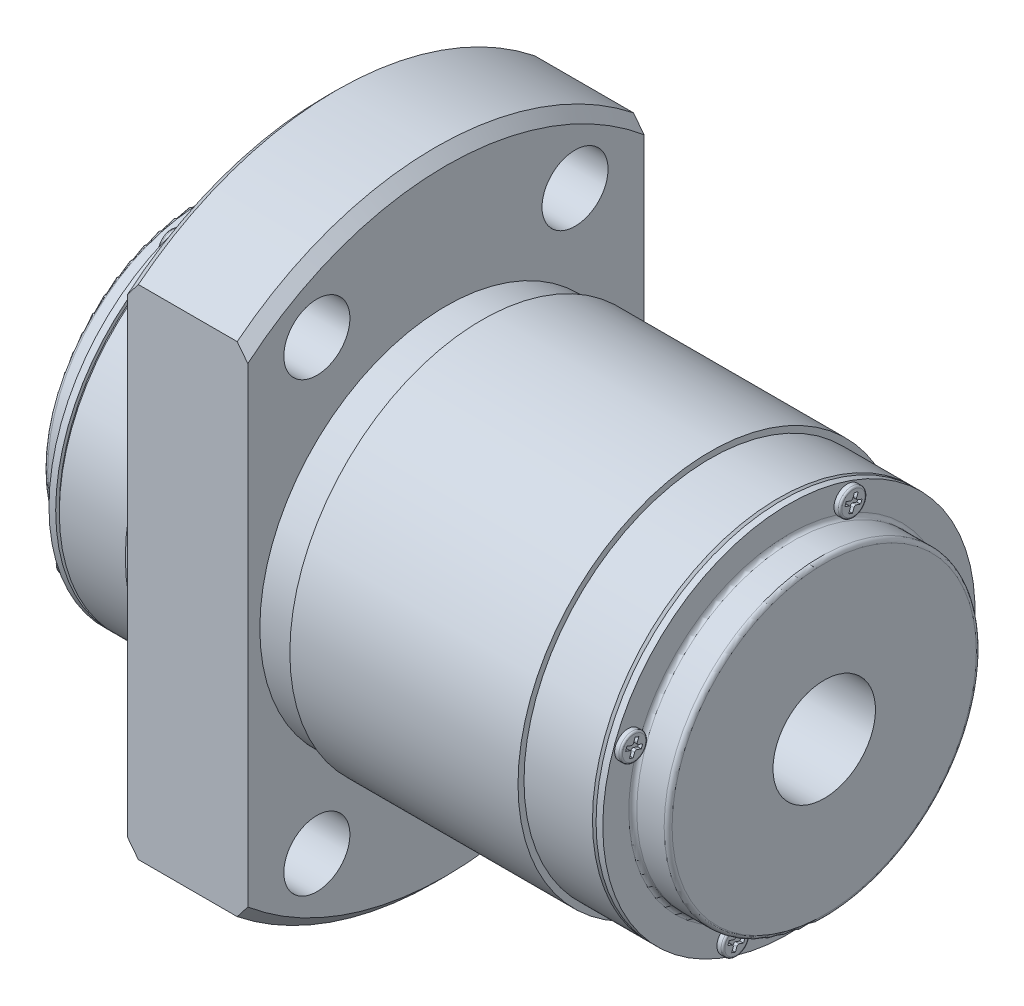
SolidWorks part; units mm, degrees
ref_plane "Front Plane" through (0, 0, 0) normal (0, 0, 1) x (1, 0, 0)
ref_plane "Top Plane" through (0, 0, 0) normal (0, 1, 0) x (1, 0, 0)
ref_plane "Right Plane" through (0, 0, 0) normal (1, 0, 0) x (0, 0, -1)
ref_plane "Plane1" through (0, 0, 0) normal (0, 0, 1) x (1, 0, 0)
sketch "Sketch1" plane through (0, 0, 0) normal (0, 0, 1) x (1, 0, 0)
  line L0 (-3.5, 7.5) -> (48.5, 7.5)
  line L1 (48.5, 7.5) -> (48.5, 12.67)
  line L2 (48.17, 13) -> (45.89, 13)
  line L3 (45.56, 13.33) -> (45.56, 15.5)
  line L4 (45.56, 15.5) -> (45, 15.5)
  line L5 (45, 15.5) -> (45, 15.2)
  line L6 (45, 15.2) -> (44.7, 15.5)
  line L7 (44.7, 15.5) -> (39, 15.5)
  line L8 (39, 15.5) -> (39, 16)
  line L9 (39, 16) -> (20, 16)
  line L10 (20, 16) -> (20, 15.5)
  line L11 (20, 15.5) -> (17, 15.5)
  line L12 (17, 15.5) -> (17, 25.6167)
  line L13 (17, 25.6167) -> (16.1167, 26.5)
  line L14 (16.1167, 26.5) -> (7.8833, 26.5)
  line L15 (7.8833, 26.5) -> (7, 25.6167)
  line L16 (7, 25.6167) -> (7, 16)
  line L17 (7, 16) -> (6.3, 16)
  line L18 (6.3, 16) -> (6.3, 15.5)
  line L19 (6.3, 15.5) -> (0.3, 15.5)
  line L20 (0.3, 15.5) -> (0, 15.2)
  line L21 (0, 15.2) -> (0, 15.5)
  line L22 (0, 15.5) -> (-0.56, 15.5)
  line L23 (-0.56, 15.5) -> (-0.56, 13.33)
  line L24 (-0.89, 13) -> (-3.17, 13)
  line L25 (-3.5, 12.67) -> (-3.5, 7.5)
  line L26 (45, 0) -> (0, 0) construction
  arc A0 (48.5, 12.67) -> (48.17, 13) centre (48.17, 12.67) ccw
  arc A1 (45.89, 13) -> (45.56, 13.33) centre (45.89, 13.33) cw
  arc A2 (-0.56, 13.33) -> (-0.89, 13) centre (-0.89, 13.33) cw
  arc A3 (-3.17, 13) -> (-3.5, 12.67) centre (-3.17, 12.67) ccw
revolve "Revolve1" add sketch "Sketch1" angle 360 about L26
ref_plane "Plane2" through (0, 0, 0) normal (0, -0.5, 0.866) x (1, 0, 0)
sketch "Sketch2" plane through (0, 0, 0) normal (0, -0.5, 0.866) x (1, 0, 0)
  line L0 (7, 21.5) -> (7, 24.25)
  line L1 (7, 24.25) -> (17, 24.25)
  line L2 (17, 24.25) -> (17, 21.5)
  line L3 (17, 21.5) -> (7, 21.5)
  line L4 (17, 21.5) -> (7, 21.5) construction
revolve "Cut-Revolve1" cut sketch "Sketch2" angle 360 about L4
ref_plane "Plane3" through (0, 0, 0) normal (0, -0.5, 0.866) x (1, 0, 0)
sketch "Sketch3" plane through (0, 0, 0) normal (0, -0.5, 0.866) x (1, 0, 0)
  line L0 (7, -21.5) -> (7, -18.75)
  line L1 (7, -18.75) -> (17, -18.75)
  line L2 (17, -18.75) -> (17, -21.5)
  line L3 (17, -21.5) -> (7, -21.5)
  line L4 (17, -21.5) -> (7, -21.5) construction
revolve "Cut-Revolve2" cut sketch "Sketch3" angle 360 about L4
ref_plane "Plane4" through (0, 0, 0) normal (0, 0.5, 0.866) x (1, 0, 0)
sketch "Sketch4" plane through (0, 0, 0) normal (0, 0.5, 0.866) x (1, 0, 0)
  line L0 (7, 21.5) -> (7, 24.25)
  line L1 (7, 24.25) -> (17, 24.25)
  line L2 (17, 24.25) -> (17, 21.5)
  line L3 (17, 21.5) -> (7, 21.5)
  line L4 (17, 21.5) -> (7, 21.5) construction
revolve "Cut-Revolve3" cut sketch "Sketch4" angle 360 about L4
ref_plane "Plane5" through (0, 0, 0) normal (0, 0.5, 0.866) x (1, 0, 0)
sketch "Sketch5" plane through (0, 0, 0) normal (0, 0.5, 0.866) x (1, 0, 0)
  line L0 (7, -21.5) -> (7, -18.75)
  line L1 (7, -18.75) -> (17, -18.75)
  line L2 (17, -18.75) -> (17, -21.5)
  line L3 (17, -21.5) -> (7, -21.5)
  line L4 (17, -21.5) -> (7, -21.5) construction
revolve "Cut-Revolve4" cut sketch "Sketch5" angle 360 about L4
ref_plane "Plane6" through (0, 0, 0) normal (0, 0, 1) x (1, 0, 0)
sketch "Sketch6" plane through (0, 0, 0) normal (0, 0, 1) x (1, 0, 0)
  line L0 (12, -5.5) -> (14.4585, -6.9194)
  line L1 (14.4585, -6.9194) -> (14.4585, -25.9585)
  line L2 (14.4585, -25.9585) -> (15, -26.5)
  line L3 (15, -26.5) -> (12, -26.5)
  line L4 (12, -26.5) -> (12, -5.5)
  line L5 (12, -26.5) -> (12, -5.5) construction
revolve "Cut-Revolve5" cut sketch "Sketch6" angle 360 about L5
ref_plane "Plane7" through (17, 0, 0) normal (1, 0, 0) x (0, 0, -1)
sketch "Sketch7" plane through (17, 0, 0) normal (1, 0, 0) x (0, 0, -1)
  line L0 (-33, 53) -> (-33, -53)
  line L1 (-33, -53) -> (33, -53)
  line L2 (33, -53) -> (33, 53)
  line L3 (33, 53) -> (-33, 53)
  line L4 (-16.5, 27.5) -> (-16.5, -27.5)
  line L5 (-16.5, -27.5) -> (16.5, -27.5)
  line L6 (16.5, -27.5) -> (16.5, 27.5)
  line L7 (16.5, 27.5) -> (-16.5, 27.5)
extrude "Cut-Extrude1" cut sketch "Sketch7" against normal blind 10
ref_plane "Plane8" through (0, 0, 0) normal (0, -0.342, 0.9397) x (1, 0, 0)
sketch "Sketch8" plane through (0, 0, 0) normal (0, -0.342, 0.9397) x (1, 0, 0)
  line L0 (-1.06, 14.25) -> (-1.06, 15.17)
  line L1 (-0.86, 15.37) -> (-0.56, 15.37)
  line L2 (-0.56, 15.37) -> (-0.56, 14.25)
  line L3 (-0.56, 14.25) -> (-1.06, 14.25)
  line L4 (-0.56, 14.25) -> (-1.06, 14.25) construction
  arc A0 (-1.06, 15.17) -> (-0.86, 15.37) centre (-0.86, 15.17) cw
revolve "Revolve2" add sketch "Sketch8" angle 360 about L4
ref_plane "Plane9" through (0, -4.8738, 13.3906) normal (0, -0.342, 0.9397) x (1, 0, 0)
sketch "Sketch9" plane through (0, -4.8738, 13.3906) normal (0, -0.342, 0.9397) x (1, 0, 0)
  line L0 (-1.06, 0) -> (-1.06, 0.92)
  line L1 (-0.86, 1.12) -> (-0.56, 1.12)
  line L2 (-0.56, 1.12) -> (-0.56, 0)
  line L3 (-0.56, 0) -> (-1.06, 0)
  line L4 (-0.56, 0) -> (-1.06, 0) construction
  arc A0 (-1.06, 0.92) -> (-0.86, 1.12) centre (-0.86, 0.92) cw
revolve "Revolve3" add sketch "Sketch9" angle 360 about L4
ref_plane "Plane10" through (0, 0, 0) normal (0, -0.342, 0.9397) x (1, 0, 0)
sketch "Sketch10" plane through (0, 0, 0) normal (0, -0.342, 0.9397) x (1, 0, 0)
  line L0 (-1.06, -14.25) -> (-1.06, -13.33)
  line L1 (-0.86, -13.13) -> (-0.56, -13.13)
  line L2 (-0.56, -13.13) -> (-0.56, -14.25)
  line L3 (-0.56, -14.25) -> (-1.06, -14.25)
  line L4 (-0.56, -14.25) -> (-1.06, -14.25) construction
  arc A0 (-1.06, -13.33) -> (-0.86, -13.13) centre (-0.86, -13.33) cw
revolve "Revolve4" add sketch "Sketch10" angle 360 about L4
ref_plane "Plane11" through (0, 4.8738, -13.3906) normal (0, -0.342, 0.9397) x (1, 0, 0)
sketch "Sketch11" plane through (0, 4.8738, -13.3906) normal (0, -0.342, 0.9397) x (1, 0, 0)
  line L0 (-1.06, 0) -> (-1.06, 0.92)
  line L1 (-0.86, 1.12) -> (-0.56, 1.12)
  line L2 (-0.56, 1.12) -> (-0.56, 0)
  line L3 (-0.56, 0) -> (-1.06, 0)
  line L4 (-0.56, 0) -> (-1.06, 0) construction
  arc A0 (-1.06, 0.92) -> (-0.86, 1.12) centre (-0.86, 0.92) cw
revolve "Revolve5" add sketch "Sketch11" angle 360 about L4
ref_plane "Plane12" through (0, 0, 0) normal (0, 0.342, 0.9397) x (1, 0, 0)
sketch "Sketch12" plane through (0, 0, 0) normal (0, 0.342, 0.9397) x (1, 0, 0)
  line L0 (45.56, 14.25) -> (45.56, 15.37)
  line L1 (45.56, 15.37) -> (45.91, 15.37)
  line L2 (46.06, 15.22) -> (46.06, 14.25)
  line L3 (46.06, 14.25) -> (45.56, 14.25)
  line L4 (46.06, 14.25) -> (45.56, 14.25) construction
  arc A0 (45.91, 15.37) -> (46.06, 15.22) centre (45.91, 15.22) cw
revolve "Revolve6" add sketch "Sketch12" angle 360 about L4
ref_plane "Plane13" through (0, -4.8738, -13.3906) normal (0, 0.342, 0.9397) x (1, 0, 0)
sketch "Sketch13" plane through (0, -4.8738, -13.3906) normal (0, 0.342, 0.9397) x (1, 0, 0)
  line L0 (45.56, 0) -> (45.56, 1.12)
  line L1 (45.56, 1.12) -> (45.91, 1.12)
  line L2 (46.06, 0.97) -> (46.06, 0)
  line L3 (46.06, 0) -> (45.56, 0)
  line L4 (46.06, 0) -> (45.56, 0) construction
  arc A0 (45.91, 1.12) -> (46.06, 0.97) centre (45.91, 0.97) cw
revolve "Revolve7" add sketch "Sketch13" angle 360 about L4
ref_plane "Plane14" through (0, 0, 0) normal (0, 0.342, 0.9397) x (1, 0, 0)
sketch "Sketch14" plane through (0, 0, 0) normal (0, 0.342, 0.9397) x (1, 0, 0)
  line L0 (45.56, -14.25) -> (45.56, -13.13)
  line L1 (45.56, -13.13) -> (45.91, -13.13)
  line L2 (46.06, -13.28) -> (46.06, -14.25)
  line L3 (46.06, -14.25) -> (45.56, -14.25)
  line L4 (46.06, -14.25) -> (45.56, -14.25) construction
  arc A0 (45.91, -13.13) -> (46.06, -13.28) centre (45.91, -13.28) cw
revolve "Revolve8" add sketch "Sketch14" angle 360 about L4
ref_plane "Plane15" through (0, 4.8738, 13.3906) normal (0, 0.342, 0.9397) x (1, 0, 0)
sketch "Sketch15" plane through (0, 4.8738, 13.3906) normal (0, 0.342, 0.9397) x (1, 0, 0)
  line L0 (45.56, 0) -> (45.56, 1.12)
  line L1 (45.56, 1.12) -> (45.91, 1.12)
  line L2 (46.06, 0.97) -> (46.06, 0)
  line L3 (46.06, 0) -> (45.56, 0)
  line L4 (46.06, 0) -> (45.56, 0) construction
  arc A0 (45.91, 1.12) -> (46.06, 0.97) centre (45.91, 0.97) cw
revolve "Revolve9" add sketch "Sketch15" angle 360 about L4
ref_plane "Plane16" through (46.06, 0, 0) normal (1, 0, 0) x (0, 0, -1)
sketch "Sketch16" plane through (46.06, 0, 0) normal (1, 0, 0) x (0, 0, -1)
  line L0 (4.1643, 13.4733) -> (4.512, 13.3467)
  line L1 (4.6076, 13.1417) -> (4.481, 12.794)
  line L2 (4.481, 12.794) -> (4.7911, 12.6811)
  line L3 (4.7911, 12.6811) -> (4.9177, 13.0288)
  line L4 (5.1228, 13.1244) -> (5.4704, 12.9979)
  line L5 (5.4704, 12.9979) -> (5.5833, 13.308)
  line L6 (5.5833, 13.308) -> (5.2356, 13.4345)
  line L7 (5.14, 13.6396) -> (5.2665, 13.9873)
  line L8 (5.2665, 13.9873) -> (4.9564, 14.1001)
  line L9 (4.9564, 14.1001) -> (4.8299, 13.7525)
  line L10 (4.6248, 13.6568) -> (4.2771, 13.7834)
  line L11 (4.2771, 13.7834) -> (4.1643, 13.4733)
  arc A0 (4.512, 13.3467) -> (4.6076, 13.1417) centre (4.4572, 13.1964) cw
  arc A1 (4.9177, 13.0288) -> (5.1228, 13.1244) centre (5.068, 12.9741) cw
  arc A2 (5.2356, 13.4345) -> (5.14, 13.6396) centre (5.2903, 13.5849) cw
  arc A3 (4.8299, 13.7525) -> (4.6248, 13.6568) centre (4.6795, 13.8072) cw
extrude "Cut-Extrude2" cut sketch "Sketch16" against normal blind 0.3
ref_plane "Plane17" through (46.06, 0, 0) normal (1, 0, 0) x (0, 0, -1)
sketch "Sketch17" plane through (46.06, 0, 0) normal (1, 0, 0) x (0, 0, -1)
  line L0 (-14.1001, 4.9564) -> (-13.7525, 4.8299)
  line L1 (-13.6568, 4.6248) -> (-13.7834, 4.2771)
  line L2 (-13.7834, 4.2771) -> (-13.4733, 4.1643)
  line L3 (-13.4733, 4.1643) -> (-13.3467, 4.512)
  line L4 (-13.1417, 4.6076) -> (-12.794, 4.481)
  line L5 (-12.794, 4.481) -> (-12.6811, 4.7911)
  line L6 (-12.6811, 4.7911) -> (-13.0288, 4.9177)
  line L7 (-13.1244, 5.1228) -> (-12.9979, 5.4704)
  line L8 (-12.9979, 5.4704) -> (-13.308, 5.5833)
  line L9 (-13.308, 5.5833) -> (-13.4345, 5.2356)
  line L10 (-13.6396, 5.14) -> (-13.9873, 5.2665)
  line L11 (-13.9873, 5.2665) -> (-14.1001, 4.9564)
  arc A0 (-13.7525, 4.8299) -> (-13.6568, 4.6248) centre (-13.8072, 4.6795) cw
  arc A1 (-13.3467, 4.512) -> (-13.1417, 4.6076) centre (-13.1964, 4.4572) cw
  arc A2 (-13.0288, 4.9177) -> (-13.1244, 5.1228) centre (-12.9741, 5.068) cw
  arc A3 (-13.4345, 5.2356) -> (-13.6396, 5.14) centre (-13.5849, 5.2903) cw
extrude "Cut-Extrude3" cut sketch "Sketch17" against normal blind 0.3
ref_plane "Plane18" through (46.06, 0, 0) normal (1, 0, 0) x (0, 0, -1)
sketch "Sketch18" plane through (46.06, 0, 0) normal (1, 0, 0) x (0, 0, -1)
  line L0 (-5.5833, -13.308) -> (-5.2356, -13.4345)
  line L1 (-5.14, -13.6396) -> (-5.2665, -13.9873)
  line L2 (-5.2665, -13.9873) -> (-4.9564, -14.1001)
  line L3 (-4.9564, -14.1001) -> (-4.8299, -13.7525)
  line L4 (-4.6248, -13.6568) -> (-4.2771, -13.7834)
  line L5 (-4.2771, -13.7834) -> (-4.1643, -13.4733)
  line L6 (-4.1643, -13.4733) -> (-4.512, -13.3467)
  line L7 (-4.6076, -13.1417) -> (-4.481, -12.794)
  line L8 (-4.481, -12.794) -> (-4.7911, -12.6811)
  line L9 (-4.7911, -12.6811) -> (-4.9177, -13.0288)
  line L10 (-5.1228, -13.1244) -> (-5.4704, -12.9979)
  line L11 (-5.4704, -12.9979) -> (-5.5833, -13.308)
  arc A0 (-5.2356, -13.4345) -> (-5.14, -13.6396) centre (-5.2903, -13.5849) cw
  arc A1 (-4.8299, -13.7525) -> (-4.6248, -13.6568) centre (-4.6795, -13.8072) cw
  arc A2 (-4.512, -13.3467) -> (-4.6076, -13.1417) centre (-4.4572, -13.1964) cw
  arc A3 (-4.9177, -13.0288) -> (-5.1228, -13.1244) centre (-5.068, -12.9741) cw
extrude "Cut-Extrude4" cut sketch "Sketch18" against normal blind 0.3
ref_plane "Plane19" through (46.06, 0, 0) normal (1, 0, 0) x (0, 0, -1)
sketch "Sketch19" plane through (46.06, 0, 0) normal (1, 0, 0) x (0, 0, -1)
  line L0 (12.6811, -4.7911) -> (13.0288, -4.9177)
  line L1 (13.1244, -5.1228) -> (12.9979, -5.4704)
  line L2 (12.9979, -5.4704) -> (13.308, -5.5833)
  line L3 (13.308, -5.5833) -> (13.4345, -5.2356)
  line L4 (13.6396, -5.14) -> (13.9873, -5.2665)
  line L5 (13.9873, -5.2665) -> (14.1001, -4.9564)
  line L6 (14.1001, -4.9564) -> (13.7525, -4.8299)
  line L7 (13.6568, -4.6248) -> (13.7834, -4.2771)
  line L8 (13.7834, -4.2771) -> (13.4733, -4.1643)
  line L9 (13.4733, -4.1643) -> (13.3467, -4.512)
  line L10 (13.1417, -4.6076) -> (12.794, -4.481)
  line L11 (12.794, -4.481) -> (12.6811, -4.7911)
  arc A0 (13.0288, -4.9177) -> (13.1244, -5.1228) centre (12.9741, -5.068) cw
  arc A1 (13.4345, -5.2356) -> (13.6396, -5.14) centre (13.5849, -5.2903) cw
  arc A2 (13.7525, -4.8299) -> (13.6568, -4.6248) centre (13.8072, -4.6795) cw
  arc A3 (13.3467, -4.512) -> (13.1417, -4.6076) centre (13.1964, -4.4572) cw
extrude "Cut-Extrude5" cut sketch "Sketch19" against normal blind 0.3
ref_plane "Plane20" through (-1.06, 0, 0) normal (1, 0, 0) x (0, 0, -1)
sketch "Sketch20" plane through (-1.06, 0, 0) normal (1, 0, 0) x (0, 0, -1)
  line L0 (-5.5833, 13.308) -> (-5.4704, 12.9979)
  line L1 (-5.4704, 12.9979) -> (-5.1228, 13.1244)
  line L2 (-4.9177, 13.0288) -> (-4.7911, 12.6811)
  line L3 (-4.7911, 12.6811) -> (-4.481, 12.794)
  line L4 (-4.481, 12.794) -> (-4.6076, 13.1417)
  line L5 (-4.512, 13.3467) -> (-4.1643, 13.4733)
  line L6 (-4.1643, 13.4733) -> (-4.2771, 13.7834)
  line L7 (-4.2771, 13.7834) -> (-4.6248, 13.6568)
  line L8 (-4.8299, 13.7525) -> (-4.9564, 14.1001)
  line L9 (-4.9564, 14.1001) -> (-5.2665, 13.9873)
  line L10 (-5.2665, 13.9873) -> (-5.14, 13.6396)
  line L11 (-5.2356, 13.4345) -> (-5.5833, 13.308)
  arc A0 (-5.1228, 13.1244) -> (-4.9177, 13.0288) centre (-5.068, 12.9741) cw
  arc A1 (-4.6076, 13.1417) -> (-4.512, 13.3467) centre (-4.4572, 13.1964) cw
  arc A2 (-4.6248, 13.6568) -> (-4.8299, 13.7525) centre (-4.6795, 13.8072) cw
  arc A3 (-5.14, 13.6396) -> (-5.2356, 13.4345) centre (-5.2903, 13.5849) cw
extrude "Cut-Extrude6" cut sketch "Sketch20" along normal blind 0.3
ref_plane "Plane21" through (-1.06, 0, 0) normal (1, 0, 0) x (0, 0, -1)
sketch "Sketch21" plane through (-1.06, 0, 0) normal (1, 0, 0) x (0, 0, -1)
  line L0 (-14.1001, -4.9564) -> (-13.9873, -5.2665)
  line L1 (-13.9873, -5.2665) -> (-13.6396, -5.14)
  line L2 (-13.4345, -5.2356) -> (-13.308, -5.5833)
  line L3 (-13.308, -5.5833) -> (-12.9979, -5.4704)
  line L4 (-12.9979, -5.4704) -> (-13.1244, -5.1228)
  line L5 (-13.0288, -4.9177) -> (-12.6811, -4.7911)
  line L6 (-12.6811, -4.7911) -> (-12.794, -4.481)
  line L7 (-12.794, -4.481) -> (-13.1417, -4.6076)
  line L8 (-13.3467, -4.512) -> (-13.4733, -4.1643)
  line L9 (-13.4733, -4.1643) -> (-13.7834, -4.2771)
  line L10 (-13.7834, -4.2771) -> (-13.6568, -4.6248)
  line L11 (-13.7525, -4.8299) -> (-14.1001, -4.9564)
  arc A0 (-13.6396, -5.14) -> (-13.4345, -5.2356) centre (-13.5849, -5.2903) cw
  arc A1 (-13.1244, -5.1228) -> (-13.0288, -4.9177) centre (-12.9741, -5.068) cw
  arc A2 (-13.1417, -4.6076) -> (-13.3467, -4.512) centre (-13.1964, -4.4572) cw
  arc A3 (-13.6568, -4.6248) -> (-13.7525, -4.8299) centre (-13.8072, -4.6795) cw
extrude "Cut-Extrude7" cut sketch "Sketch21" along normal blind 0.3
ref_plane "Plane22" through (-1.06, 0, 0) normal (1, 0, 0) x (0, 0, -1)
sketch "Sketch22" plane through (-1.06, 0, 0) normal (1, 0, 0) x (0, 0, -1)
  line L0 (4.1643, -13.4733) -> (4.2771, -13.7834)
  line L1 (4.2771, -13.7834) -> (4.6248, -13.6568)
  line L2 (4.8299, -13.7525) -> (4.9564, -14.1001)
  line L3 (4.9564, -14.1001) -> (5.2665, -13.9873)
  line L4 (5.2665, -13.9873) -> (5.14, -13.6396)
  line L5 (5.2356, -13.4345) -> (5.5833, -13.308)
  line L6 (5.5833, -13.308) -> (5.4704, -12.9979)
  line L7 (5.4704, -12.9979) -> (5.1228, -13.1244)
  line L8 (4.9177, -13.0288) -> (4.7911, -12.6811)
  line L9 (4.7911, -12.6811) -> (4.481, -12.794)
  line L10 (4.481, -12.794) -> (4.6076, -13.1417)
  line L11 (4.512, -13.3467) -> (4.1643, -13.4733)
  arc A0 (4.6248, -13.6568) -> (4.8299, -13.7525) centre (4.6795, -13.8072) cw
  arc A1 (5.14, -13.6396) -> (5.2356, -13.4345) centre (5.2903, -13.5849) cw
  arc A2 (5.1228, -13.1244) -> (4.9177, -13.0288) centre (5.068, -12.9741) cw
  arc A3 (4.6076, -13.1417) -> (4.512, -13.3467) centre (4.4572, -13.1964) cw
extrude "Cut-Extrude8" cut sketch "Sketch22" along normal blind 0.3
ref_plane "Plane23" through (-1.06, 0, 0) normal (1, 0, 0) x (0, 0, -1)
sketch "Sketch23" plane through (-1.06, 0, 0) normal (1, 0, 0) x (0, 0, -1)
  line L0 (12.6811, 4.7911) -> (12.794, 4.481)
  line L1 (12.794, 4.481) -> (13.1417, 4.6076)
  line L2 (13.3467, 4.512) -> (13.4733, 4.1643)
  line L3 (13.4733, 4.1643) -> (13.7834, 4.2771)
  line L4 (13.7834, 4.2771) -> (13.6568, 4.6248)
  line L5 (13.7525, 4.8299) -> (14.1001, 4.9564)
  line L6 (14.1001, 4.9564) -> (13.9873, 5.2665)
  line L7 (13.9873, 5.2665) -> (13.6396, 5.14)
  line L8 (13.4345, 5.2356) -> (13.308, 5.5833)
  line L9 (13.308, 5.5833) -> (12.9979, 5.4704)
  line L10 (12.9979, 5.4704) -> (13.1244, 5.1228)
  line L11 (13.0288, 4.9177) -> (12.6811, 4.7911)
  arc A0 (13.1417, 4.6076) -> (13.3467, 4.512) centre (13.1964, 4.4572) cw
  arc A1 (13.6568, 4.6248) -> (13.7525, 4.8299) centre (13.8072, 4.6795) cw
  arc A2 (13.6396, 5.14) -> (13.4345, 5.2356) centre (13.5849, 5.2903) cw
  arc A3 (13.1244, 5.1228) -> (13.0288, 4.9177) centre (12.9741, 5.068) cw
extrude "Cut-Extrude9" cut sketch "Sketch23" along normal blind 0.3
sketch "Sketch24" plane through (-3.5, 0, 0) normal (-1, 0, 0) x (0, 0, 1)
  circle A0 centre (0, 0) radius 7.5
  circle A1 centre (0, 0) radius 4.2667
  dimension "D1" = 8.5333
extrude "Boss-Extrude1" add sketch "Sketch24" against normal up to surface (52 mm away) up to face at (48.5, 0, 12.67)
scale "Scale1" scale about centroid uniform scaling yes scale factor 7.5
